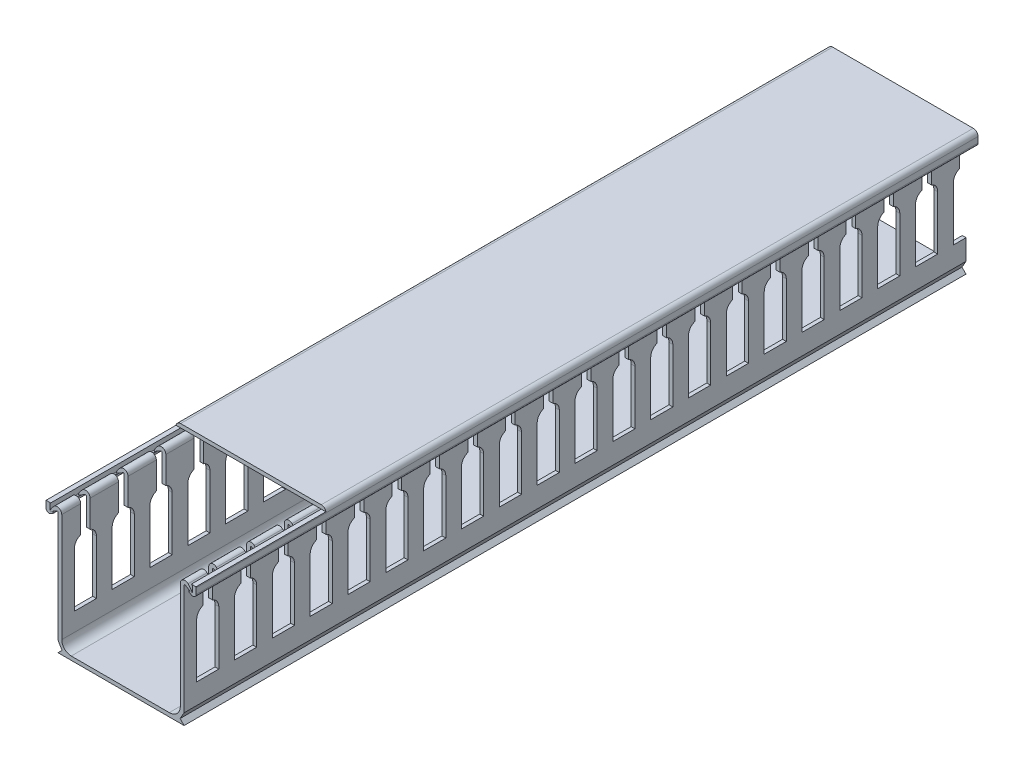
SolidWorks part; units mm, degrees
ref_plane "Front Plane" through (0, 0, 0) normal (0, 0, 1) x (1, 0, 0)
ref_plane "Top Plane" through (0, 0, 0) normal (0, 1, 0) x (1, 0, 0)
ref_plane "Right Plane" through (0, 0, 0) normal (1, 0, 0) x (0, 0, -1)
sketch "Sketch1" plane through (0, 0, 0) normal (0, 0, 1) x (1, 0, 0)
  line L0 (-20, 0) -> (20, 0)
  line L1 (-20, 3.5) -> (-20, 38.546)
  line L2 (-20, 0) -> (-18.7189, 1.2811)
  line L3 (-18.7189, 1.2811) -> (-20, 3.5)
  line L4 (-22.4196, 37.589) -> (-20.381, 38.766)
  line L5 (0, 0) -> (0, -17.0643) construction
  line L6 (22.4196, 37.589) -> (22.5, 37.889)
  line L7 (22.4196, 37.589) -> (20.381, 38.766)
  line L8 (20, 3.5) -> (20, 38.546)
  line L9 (18.7189, 1.2811) -> (20, 3.5)
  line L10 (-22.4196, 37.589) -> (-22.5, 37.889)
  line L11 (20, 0) -> (18.7189, 1.2811)
  line L12 (-18.8, 4.2) -> (-18.8, 38.546)
  line L13 (18.8, 3.5) -> (18.8, 38.546) construction
  line L14 (-17.2865, 1.2) -> (20, 1.2) construction
  line L15 (-15.8, 1.2) -> (15.3, 1.2)
  line L16 (18.8, 4.7) -> (18.8, 38.546)
  line L17 (-17.2865, 1.2) -> (-18.8, 3.8215) construction
  line L18 (-17.2865, 1.2) -> (-17.2865, 1.2) construction
  line L19 (-18.8, 3.8215) -> (-18.8, 38.546) construction
  arc A0 (-22.5, 37.889) -> (-21.2623, 39.5936) centre (-17.1014, 35.2708) cw
  arc A1 (22.5, 37.889) -> (21.2623, 39.5936) centre (17.1014, 35.2708) ccw
  arc A2 (20.381, 38.766) -> (20, 38.546) centre (20.254, 38.546) ccw
  arc A3 (-21.2623, 39.5936) -> (-18.8, 38.546) centre (-20.254, 38.546) cw
  arc A4 (21.2623, 39.5936) -> (18.8, 38.546) centre (20.254, 38.546) ccw
  arc A5 (-15.8, 1.2) -> (-18.8, 4.2) centre (-15.8, 4.2) cw
  arc A6 (-20.381, 38.766) -> (-20, 38.546) centre (-20.254, 38.546) cw
  arc A7 (15.3, 1.2) -> (18.8, 4.7) centre (15.3, 4.7) ccw
  arc A8 (-20.981, 39.8052) -> (-18.8, 38.546) centre (-20.254, 38.546) cw construction
  arc A9 (20.981, 39.8052) -> (18.8, 38.546) centre (20.254, 38.546) ccw construction
  dimension "D1" = 0.3
  dimension "D2" = 6
  dimension "D3" = 60
  dimension "D5" = 0.254
  dimension "D6" = 1.2
  dimension "D11" = 3
  dimension "D13" = 3.5
  dimension "D14" = 40
  dimension "D7" = 45
  dimension "D8" = 30
  dimension "D4" = 75
  dimension "D9" = 3.5
  dimension "D10" = 2.5
  dimension "D12" = 40
extrude "Boss-Extrude2" add sketch "Sketch1" along normal mid plane 1000 contours L0 L11 L9 L8 A2 L7 L6 A1 A4 L16 A7 L15 A5 L12 A3 A0 L10 L4 A6 L1 L3 L2
sketch "Sketch2" plane through (0, 0, 0) normal (1, 0, 0) x (0, 0, -1)
  line L0 (490, 30) -> (490, 40)
  line L1 (-500, 0) -> (500, 0) construction
  line L2 (500, 3.5) -> (500, 38.546) construction
  line L3 (488, 10) -> (495, 10)
  line L4 (495, 10) -> (495, 27.1716)
  line L6 (490, 40) -> (493, 40)
  line L7 (493, 30) -> (493, 40)
  line L8 (488, 10) -> (488, 27.1716)
  line L10 (500, 40) -> (-500, 40) construction
  arc A0 (495, 27.1716) -> (493, 30) centre (492, 27.1716) ccw
  arc A1 (488, 27.1716) -> (490, 30) centre (491, 27.1716) cw
  point P22 (491.5, 10)
  point P23 (491.5, 40)
  dimension "D1" = 3
  dimension "D2" = 10
  dimension "D3" = 10
  dimension "D4" = 7
  dimension "D5" = 5
  dimension "D6" = 3
extrude "Cut-Extrude1" cut sketch "Sketch2" against normal blind 82.296 and the other way blind 151.13
pattern_linear "LPattern1" count 83 spacing 12 along (0, 0, 1) of "Cut-Extrude1"
sketch "Sketch3" plane through (0, 0, -500) normal (0, 0, 1) x (1, 0, 0)
  line L0 (-22.6, 37.9) -> (-22.6, 39.7) construction
  line L1 (-22.6, 37.8781) -> (-22.6, 39.7)
  line L2 (22.3, 40) -> (-22.3, 40)
  line L4 (22.6, 37.8781) -> (22.6, 39.7)
  line L5 (22.6, 37.9) -> (22.6, 39.7) construction
  line L6 (22.3, 41.2) -> (-22.3, 41.2)
  line L7 (-22.3, 37.034) -> (-21.6, 37.4381)
  line L8 (-21.6, 37.4381) -> (-21.6, 38.0155)
  line L9 (-23.8, 37.9) -> (-23.8, 39.7)
  line L10 (-21.6, 38.0155) -> (-22.219, 37.6581)
  line L12 (22.3, 37.034) -> (21.6, 37.4381)
  line L14 (21.6, 38.0155) -> (22.219, 37.6581)
  line L15 (23.8, 37.9) -> (23.8, 39.7)
  line L16 (21.6, 37.4381) -> (21.6, 38.0155)
  arc A0 (-23.8, 37.9) -> (-22.3, 37.034) centre (-22.8, 37.9) ccw
  arc A1 (-22.6, 37.8781) -> (-22.219, 37.6581) centre (-22.346, 37.8781) ccw
  arc A2 (22.3, 37.034) -> (23.8, 37.9) centre (22.8, 37.9) ccw
  arc A3 (-22.3, 41.2) -> (-23.8, 39.7) centre (-22.3, 39.7) ccw
  arc A4 (-22.3, 40) -> (-22.6, 39.7) centre (-22.3, 39.7) ccw
  arc A5 (22.3, 41.2) -> (23.8, 39.7) centre (22.3, 39.7) cw
  arc A6 (22.3, 40) -> (22.6, 39.7) centre (22.3, 39.7) cw
  arc A7 (22.6, 37.8781) -> (22.219, 37.6581) centre (22.346, 37.8781) cw
  arc A9 (-18.8, 38.546) -> (-21.2623, 39.5936) centre (-20.254, 38.546) ccw construction
  point P35 (0, 40)
  dimension "D2" = 2.2
  dimension "D3" = 0.254
  dimension "D4" = 2.2
  dimension "D5" = 1.5
  dimension "D7" = 4.3
  dimension "D12" = 1
  dimension "D6" = 60
  dimension "D8" = 60
  dimension "D9" = 0.5
  dimension "D11" = 0.1
  dimension "D10" = 1.2
extrude "Boss-Extrude3" add sketch "Sketch3" along normal up to vertex (1000 mm away) separate body
sketch "Sketch4" plane through (0, 0, -500) normal (0, 0, -1) x (-1, 0, 0)
  line L1 (-24.9226, 42.1939) -> (24.0691, 42.1939)
  line L2 (-24.9226, 42.1939) -> (-24.9226, -1.5913)
  line L3 (-24.9226, -1.5913) -> (24.0691, -1.5913)
  line L4 (24.0691, 42.1939) -> (24.0691, -1.5913)
extrude "Cut-Extrude2" cut sketch "Sketch4" against normal blind 752
sketch "Sketch8" plane through (0, 0, 500) normal (0, 0, 1) x (1, 0, 0)
  line L1 (-23.7697, 40) -> (23.8, 40)
  line L2 (-23.7697, 40) -> (-23.7697, 41.2)
  line L3 (-23.7697, 41.2) -> (23.8, 41.2)
  line L4 (23.8, 40) -> (23.8, 41.2)
  arc A0 (-22.3, 41.2) -> (-23.8, 39.7) centre (-22.3, 39.7) ccw construction
extrude "Cut-Extrude4" cut sketch "Sketch8" against normal blind 41.2
